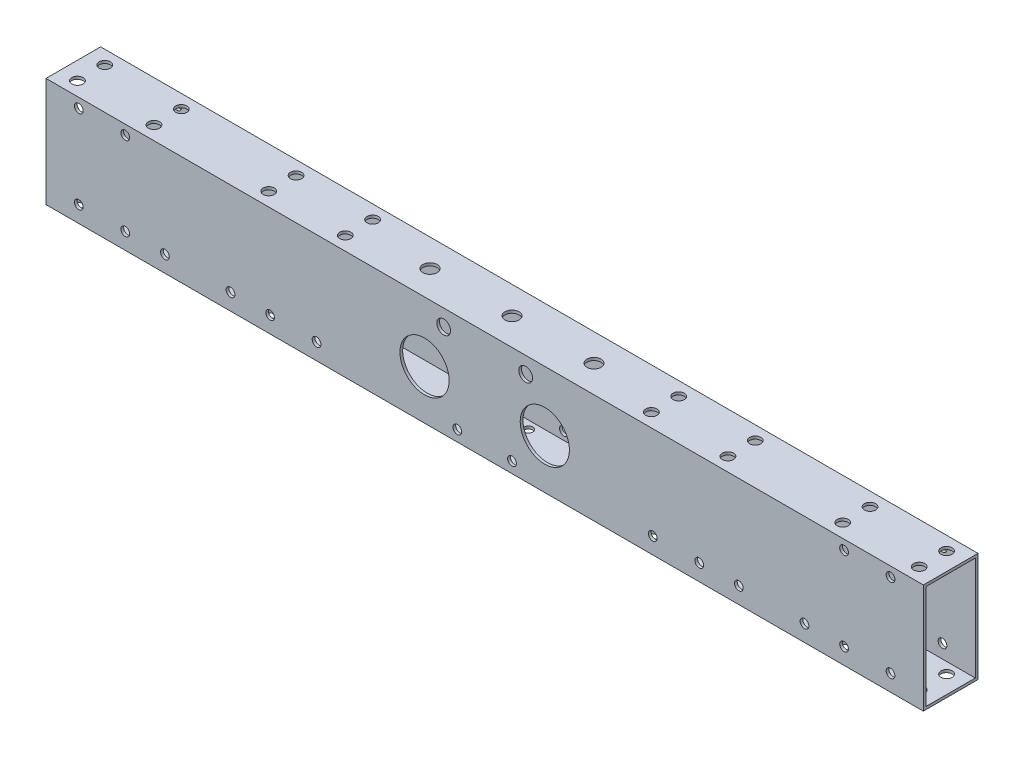
SolidWorks part; units mm, degrees
material "6061-T6 (SS)"
ref_plane "前视基准面" through (0, 0, 0) normal (0, 0, 1) x (1, 0, 0)
ref_plane "上视基准面" through (0, 0, 0) normal (0, 1, 0) x (1, 0, 0)
ref_plane "右视基准面" through (0, 0, 0) normal (1, 0, 0) x (0, 0, -1)
sketch "草图1" plane through (0, 0, 0) normal (1, 0, 0) x (0, 0, -1)
  line L0 (9, 19) -> (9, -19)
  line L1 (10, 20) -> (-10, 20)
  line L2 (10, 20) -> (10, -20)
  line L3 (10, -20) -> (-10, -20)
  line L4 (-10, 20) -> (-10, -20)
  line L5 (10, 20) -> (-10, -20) construction
  line L6 (10, -20) -> (-10, 20) construction
  line L7 (9, -19) -> (-9, -19)
  line L8 (-9, 19) -> (-9, -19)
  line L9 (9, 19) -> (-9, 19)
  point P0 (0, 0)
  dimension "D1" = 40
  dimension "D2" = 20
  dimension "D3" = 1
extrude "凸台-拉伸1" add sketch "草图1" along normal blind 321
sketch "草图2" plane through (0, 20, 0) normal (0, 1, 0) x (1, 0, 0)
  line L0 (160.5, 10) -> (160.5, -10) construction
  line L1 (321, 10) -> (0, 10) construction
  line L2 (321, -10) -> (0, -10) construction
  line L4 (104.5, 5) -> (76.5, 5) construction
  line L5 (104.5, 5) -> (104.5, -5) construction
  line L6 (104.5, -5) -> (76.5, -5) construction
  line L7 (76.5, 5) -> (76.5, -5) construction
  line L8 (104.5, 5) -> (76.5, -5) construction
  line L9 (104.5, -5) -> (76.5, 5) construction
  circle A0 centre (76.5, 5) radius 2.05
  circle A1 centre (76.5, -5) radius 2.05
  circle A2 centre (104.5, -5) radius 2.05
  circle A3 centre (104.5, 5) radius 2.05
  circle A4 centre (216.5, -5) radius 2.05
  circle A5 centre (216.5, 5) radius 2.05
  circle A6 centre (244.5, -5) radius 2.05
  circle A7 centre (244.5, 5) radius 2.05
  point P6 (90.5, 0)
  point P16 (160.5, 0)
  dimension "D3" = 4.1
  dimension "D1" = 140
  dimension "D2" = 10
  dimension "D4" = 28
extrude "切除-拉伸1" cut sketch "草图2" against normal through all
sketch "草图3" plane through (0, -20, 0) normal (0, -1, 0) x (1, 0, 0)
  circle A0 centre (76.5, 5) radius 3.75
  circle A1 centre (76.5, -5) radius 3.75
  circle A2 centre (104.5, 5) radius 3.75
  circle A3 centre (104.5, -5) radius 3.75
  circle A4 centre (216.5, 5) radius 3.75
  circle A5 centre (244.5, 5) radius 3.75
  circle A6 centre (244.5, -5) radius 3.75
  circle A7 centre (216.5, -5) radius 3.75
  dimension "D1" = 7.5
extrude "切除-拉伸2" [suppressed] cut sketch "草图3" against normal up to next
sketch "草图5" plane through (0, 0, 10) normal (0, 0, 1) x (1, 0, 0)
  line L0 (0, -20) -> (10.718, 20)
  line L1 (321, 20) -> (0, 20) construction
  line L2 (10.718, 20) -> (0, 20)
  line L3 (0, 20) -> (0, -20)
  line L4 (321, -20) -> (321, 20)
  line L5 (321, 20) -> (310.282, 20)
  line L6 (310.282, 20) -> (321, -20)
  line L8 (321, -20) -> (0, -20) construction
  dimension "D1" = 75
extrude "切除-拉伸3" [suppressed] cut sketch "草图5" against normal through all
sketch "草图4" [suppressed] plane through (0, 20, 0) normal (0, 1, 0) x (1, 0, 0)
  line L0 (160.5, 10) -> (160.5, -10) construction
  line L1 (310.282, 10) -> (10.718, 10) construction
  line L2 (310.282, -10) -> (10.718, -10) construction
  line L4 (60.718, 4) -> (20.718, 4) construction
  line L5 (60.718, 4) -> (60.718, -4) construction
  line L6 (60.718, -4) -> (20.718, -4) construction
  line L7 (20.718, 4) -> (20.718, -4) construction
  line L8 (60.718, 4) -> (20.718, -4) construction
  line L9 (60.718, -4) -> (20.718, 4) construction
  line L10 (10.718, 10) -> (10.718, -10) construction
  circle A0 centre (20.718, 4) radius 2.1
  circle A1 centre (20.718, -4) radius 2.1
  circle A2 centre (40.718, 4) radius 2.1
  circle A3 centre (40.718, -4) radius 2.1
  circle A4 centre (60.718, 4) radius 2.1
  circle A5 centre (60.718, -4) radius 2.1
  circle A6 centre (300.282, -4) radius 2.1
  circle A7 centre (280.282, -4) radius 2.1
  circle A8 centre (260.282, -4) radius 2.1
  circle A9 centre (260.282, 4) radius 2.1
  circle A10 centre (280.282, 4) radius 2.1
  circle A11 centre (300.282, 4) radius 2.1
  point P6 (40.718, 0)
  point P12 (160.5, 0)
  dimension "D4" = 4.2
  dimension "D1" = 8
  dimension "D2" = 40
  dimension "D3" = 10
extrude "切除-拉伸4" [suppressed] cut sketch "草图4" against normal through all
sketch "草图6" plane through (0, -20, 0) normal (0, -1, 0) x (1, 0, 0)
  line L0 (160.5, 10) -> (160.5, -10) construction
  line L1 (321, 10) -> (0, 10) construction
  line L2 (321, -10) -> (0, -10) construction
  line L4 (180.5, 6) -> (140.5, 6) construction
  line L5 (180.5, 6) -> (180.5, -6) construction
  line L6 (180.5, -6) -> (140.5, -6) construction
  line L7 (140.5, 6) -> (140.5, -6) construction
  line L8 (180.5, 6) -> (140.5, -6) construction
  line L9 (180.5, -6) -> (140.5, 6) construction
  circle A0 centre (140.5, 6) radius 1.6
  circle A1 centre (160.5, 6) radius 1.6
  circle A2 centre (180.5, 6) radius 1.6
  circle A3 centre (180.5, -6) radius 1.6
  circle A4 centre (160.5, -6) radius 1.6
  circle A5 centre (140.5, -6) radius 1.6
  point P6 (160.5, 0)
  dimension "D3" = 3.2
  dimension "D1" = 40
  dimension "D2" = 4
extrude "切除-拉伸5" cut sketch "草图6" against normal up to next
sketch "草图7" plane through (0, 0, 10) normal (0, 0, 1) x (1, 0, 0)
  line L0 (160.5, -20) -> (160.5, 20) construction
  line L1 (321, -20) -> (0, -20) construction
  line L2 (321, 20) -> (0, 20) construction
  line L3 (130.5, -16) -> (150.5, -16) construction
  line L4 (150.5, -16) -> (170.5, -16) construction
  line L5 (140.5, 2) -> (180.5, 2) construction
  line L6 (140.5, 8) -> (180.5, 8)
  line L7 (140.5, -4) -> (180.5, -4)
  circle A0 centre (130.5, -16) radius 1.6 construction
  circle A1 centre (150.5, -16) radius 1.6
  circle A2 centre (170.5, -16) radius 1.6
  circle A3 centre (190.5, -16) radius 1.6 construction
  arc A4 (140.5, 8) -> (140.5, -4) centre (140.5, 2) ccw
  arc A5 (180.5, -4) -> (180.5, 8) centre (180.5, 2) ccw
  point P8 (160.5, -16)
  point P19 (160.5, 2)
  dimension "D1" = 3.2
  dimension "D6" = 6
  dimension "D3" = 20
  dimension "D4" = 4
  dimension "D5" = 40
  dimension "D7" = 18
  dimension "D2" = 4
extrude "切除-拉伸6" [suppressed] cut sketch "草图7" against normal through all both and the other way through all
sketch "草图9" plane through (0, 0, 10) normal (0, 0, 1) x (1, 0, 0)
  line L0 (160.5, 20) -> (160.5, -20) construction
  line L1 (321, 20) -> (0, 20) construction
  line L2 (321, -20) -> (0, -20) construction
  line L3 (55.5, 0) -> (5.5, 0) construction
  line L4 (50.5, 16) -> (10.5, 16) construction
  line L5 (50.5, 16) -> (50.5, -16) construction
  line L6 (50.5, -16) -> (10.5, -16) construction
  line L7 (10.5, 16) -> (10.5, -16) construction
  line L8 (50.5, 16) -> (10.5, -16) construction
  line L9 (50.5, -16) -> (10.5, 16) construction
  line L10 (55.5, -6) -> (5.5, -6)
  line L11 (55.5, 6) -> (5.5, 6)
  line L12 (265.5, 0) -> (315.5, 0) construction
  line L13 (265.5, -6) -> (315.5, -6)
  line L14 (265.5, 6) -> (315.5, 6)
  circle A0 centre (10.5, 16) radius 1.6
  circle A1 centre (30.5, 16) radius 1.6
  circle A2 centre (50.5, 16) radius 1.6
  circle A3 centre (50.5, -16) radius 1.6
  circle A4 centre (30.5, -16) radius 1.6
  circle A5 centre (10.5, -16) radius 1.6
  arc A6 (55.5, -6) -> (55.5, 6) centre (55.5, 0) ccw
  arc A7 (5.5, 6) -> (5.5, -6) centre (5.5, 0) ccw
  arc A8 (265.5, -6) -> (265.5, 6) centre (265.5, 0) cw
  arc A9 (315.5, 6) -> (315.5, -6) centre (315.5, 0) cw
  circle A10 centre (270.5, -16) radius 1.6
  circle A11 centre (290.5, -16) radius 1.6
  circle A12 centre (310.5, -16) radius 1.6
  circle A13 centre (310.5, 16) radius 1.6
  circle A14 centre (290.5, 16) radius 1.6
  circle A15 centre (270.5, 16) radius 1.6
  point P6 (30.5, 0)
  point P12 (160.5, 0)
  point P22 (30.5, 0)
  point P31 (290.5, 0)
  dimension "D4" = 3.2
  dimension "D5" = 6
  dimension "D1" = 4
  dimension "D2" = 40
  dimension "D3" = 110
  dimension "D6" = 50
extrude "切除-拉伸7" [suppressed] cut sketch "草图9" against normal through all
sketch "草图10" plane through (0, 20, 0) normal (0, 1, 0) x (1, 0, 0)
  line L0 (160.5, 10) -> (160.5, -10) construction
  line L1 (40.5, 6) -> (20.5, 6) construction
  line L2 (40.5, 6) -> (40.5, -6) construction
  line L3 (40.5, -6) -> (20.5, -6) construction
  line L4 (20.5, 6) -> (20.5, -6) construction
  line L5 (40.5, 6) -> (20.5, -6) construction
  line L6 (40.5, -6) -> (20.5, 6) construction
  line L7 (321, 10) -> (0, 10) construction
  line L8 (321, -10) -> (0, -10) construction
  circle A0 centre (20.5, 6) radius 1.6
  circle A1 centre (20.5, -6) radius 1.6
  circle A2 centre (40.5, -6) radius 1.6
  circle A3 centre (40.5, 6) radius 1.6
  circle A4 centre (280.5, -6) radius 1.6
  circle A5 centre (280.5, 6) radius 1.6
  circle A6 centre (300.5, -6) radius 1.6
  circle A7 centre (300.5, 6) radius 1.6
  point P0 (30.5, 0)
  point P12 (160.5, 0)
  dimension "D4" = 3.2
  dimension "D1" = 20
  dimension "D2" = 4
  dimension "D3" = 120
extrude "切除-拉伸8" [suppressed] cut sketch "草图10" against normal through all
sketch "草图11" [suppressed] plane through (0, 20, 0) normal (0, 1, 0) x (1, 0, 0)
  line L0 (70.45, 10) -> (70.45, -10)
  line L3 (449.282, 10) -> (10.718, 10) construction
  line L4 (449.282, -10) -> (10.718, -10) construction
  line L5 (10.45, 9) -> (10.45, -9) construction
  dimension "D1" = 60
sketch "草图12" plane through (0, 20, 0) normal (0, 1, 0) x (1, 0, 0)
  line L0 (160.5, 10) -> (160.5, -49990) construction
  line L1 (321, 10) -> (0, 10) construction
  line L2 (0, 0) -> (-50000, 0) construction
  line L3 (0, 10) -> (0, -10) construction
  line L4 (130.5, 0) -> (160.5, 0) construction
  circle A0 centre (130.5, 0) radius 2.6
  circle A1 centre (160.5, 0) radius 2.6
  circle A2 centre (190.5, 0) radius 2.6
  point P4 (160.5, 10)
  point P9 (0, 0)
  dimension "D1" = 5.2
  dimension "D2" = 30
  dimension "D4" = 30
  dimension "D3" = 3
extrude "切除-拉伸9" cut sketch "草图12" against normal up to next
sketch "草图13" plane through (0, 0, 10) normal (0, 0, 1) x (1, 0, 0)
  line L0 (246.55, 20) -> (242.45, 20) construction
  line L1 (246.55, 20) -> (242.45, 20) construction
  line L2 (218.55, 20) -> (214.45, 20) construction
  line L3 (218.55, 20) -> (214.45, 20) construction
  line L4 (214.45, 20) -> (218.55, 20) construction
  line L5 (214.45, 20) -> (214.45, -20) construction
  line L6 (218.55, 20) -> (218.55, -20) construction
  line L7 (214.45, -20) -> (218.55, -20) construction
  line L8 (242.45, 20) -> (246.55, 20) construction
  line L9 (242.45, 20) -> (242.45, -20) construction
  line L10 (246.55, 20) -> (246.55, -20) construction
  line L11 (242.45, -20) -> (246.55, -20) construction
  line L12 (321, -20) -> (0, -20) construction
  line L13 (218.55, 20) -> (242.45, 20) construction
  line L14 (311, 20) -> (311, -49980) construction
  line L15 (321, 0) -> (50321, 0) construction
  line L16 (321, 20) -> (321, -20) construction
  line L17 (311, 13) -> (311, 0) construction
  line L18 (311, 13) -> (287, 13) construction
  line L19 (160.5, 20) -> (160.5, -49980) construction
  line L20 (321, 20) -> (0, 20) construction
  circle A0 centre (311, 13) radius 2.1
  circle A1 centre (311, 0) radius 2.1
  circle A2 centre (311, -13) radius 2.1
  circle A3 centre (287, 13) radius 2.1
  circle A4 centre (287, 0) radius 2.1
  circle A5 centre (287, -13) radius 2.1
  circle A6 centre (10, 13) radius 2.1
  circle A7 centre (10, 0) radius 2.1
  circle A8 centre (10, -13) radius 2.1
  circle A9 centre (34, -13) radius 2.1
  circle A10 centre (34, 0) radius 2.1
  circle A11 centre (34, 13) radius 2.1
  point P17 (321, 0)
  point P38 (160.5, 20)
  dimension "D1" = 4.2
  dimension "D2" = 13
  dimension "D4" = 13
  dimension "D6" = 24
  dimension "D7" = 10
  dimension "D3" = 3
  dimension "D5" = 2
sketch "草图14" plane through (0, 20, 0) normal (0, 1, 0) x (1, 0, 0)
  line L0 (160.5, 10) -> (160.5, -49990) construction
  line L1 (321, 10) -> (0, 10) construction
  line L2 (321, 0) -> (50321, 0) construction
  line L3 (321, 10) -> (321, -10) construction
  line L5 (286.5, 5) -> (314.5, 5) construction
  line L6 (286.5, 5) -> (286.5, -5) construction
  line L7 (286.5, -5) -> (314.5, -5) construction
  line L8 (314.5, 5) -> (314.5, -5) construction
  line L9 (300.5, -5) -> (300.5, 5) construction
  line L10 (286.5, 0) -> (314.5, 0) construction
  circle A0 centre (314.5, 5) radius 2.05
  circle A1 centre (314.5, -5) radius 2.05
  circle A2 centre (286.5, -5) radius 2.05
  circle A3 centre (286.5, 5) radius 2.05
  circle A4 centre (34.5, -5) radius 2.05
  circle A5 centre (6.5, -5) radius 2.05
  circle A6 centre (6.5, 5) radius 2.05
  circle A7 centre (34.5, 5) radius 2.05
  point P4 (160.5, 10)
  point P9 (321, 0)
  point P10 (300.5, 0)
  dimension "D4" = 4.1
  dimension "D1" = 10
  dimension "D2" = 28
  dimension "D3" = 140
extrude "切除-拉伸11" cut sketch "草图14" against normal through all
extrude "切除-拉伸10" [suppressed] cut sketch "草图13" against normal through all
sketch "草图15" plane through (0, 0, 10) normal (0, 0, 1) x (1, 0, 0)
  line L0 (160.5, 20) -> (160.5, -49980) construction
  line L1 (321, 20) -> (0, 20) construction
  circle A0 centre (145.5, 14) radius 2.525
  circle A1 centre (175.5, 14) radius 2.525
  point P4 (160.5, 20)
  dimension "D1" = 5.05
  dimension "D2" = 6
  dimension "D3" = 15
extrude "切除-拉伸12" cut sketch "草图15" against normal through all
sketch "草图17" plane through (0, 0, 10) normal (0, 0, 1) x (1, 0, 0)
  line L0 (160.5, 20) -> (160.5, -49980) construction
  line L1 (321, 20) -> (0, 20) construction
  line L2 (222, -14) -> (-49778, -14) construction
  line L3 (321, -20) -> (0, -20) construction
  line L4 (292, 16.5) -> (-49708, 16.5) construction
  line L5 (321, 20) -> (321, -20) construction
  circle A0 centre (12, 16.5) radius 1.6
  circle A1 centre (29, 16.5) radius 1.6
  circle A2 centre (12, -14) radius 1.6
  circle A3 centre (29, -14) radius 1.6
  circle A4 centre (43.5, -14) radius 1.6
  circle A5 centre (67.5, -14) radius 1.6
  circle A6 centre (222, -14) radius 1.6
  circle A7 centre (239, -14) radius 1.6
  circle A8 centre (253.5, -14) radius 1.6
  circle A9 centre (277.5, -14) radius 1.6
  circle A10 centre (292, -14) radius 1.6
  circle A11 centre (309, -14) radius 1.6
  circle A12 centre (82, -14) radius 1.6
  circle A13 centre (99, -14) radius 1.6
  circle A14 centre (292, 16.5) radius 1.6
  circle A15 centre (309, 16.5) radius 1.6
  circle A16 centre (150.5, -16) radius 1.6
  circle A17 centre (170.5, -16) radius 1.6
  point P9 (160.5, 20)
  dimension "D2" = 3.5
  dimension "3" = 3.2
  dimension "D13" = 3.2
  dimension "D1" = 6
  dimension "D3" = 12
  dimension "D4" = 17
  dimension "D5" = 61.5
  dimension "D6" = 17
  dimension "D7" = 14.5
  dimension "D8" = 12
  dimension "D9" = 17
  dimension "D10" = 14.5
  dimension "D11" = 10
  dimension "D12" = 4
extrude "切除-拉伸13" cut sketch "草图17" against normal through all
sketch "草图18" plane through (0, 0, 10) normal (0, 0, 1) x (1, 0, 0)
  line L0 (160.5, 20) -> (160.5, -20) construction
  line L1 (321, 20) -> (0, 20) construction
  line L2 (321, -20) -> (0, -20) construction
  circle A2 centre (138.5, -2) radius 9
  circle A3 centre (182.5, -2) radius 9
  dimension "D1" = 18
  dimension "D2" = 18
  dimension "D3" = 22
extrude "切除-拉伸14" cut sketch "草图18" against normal through all
